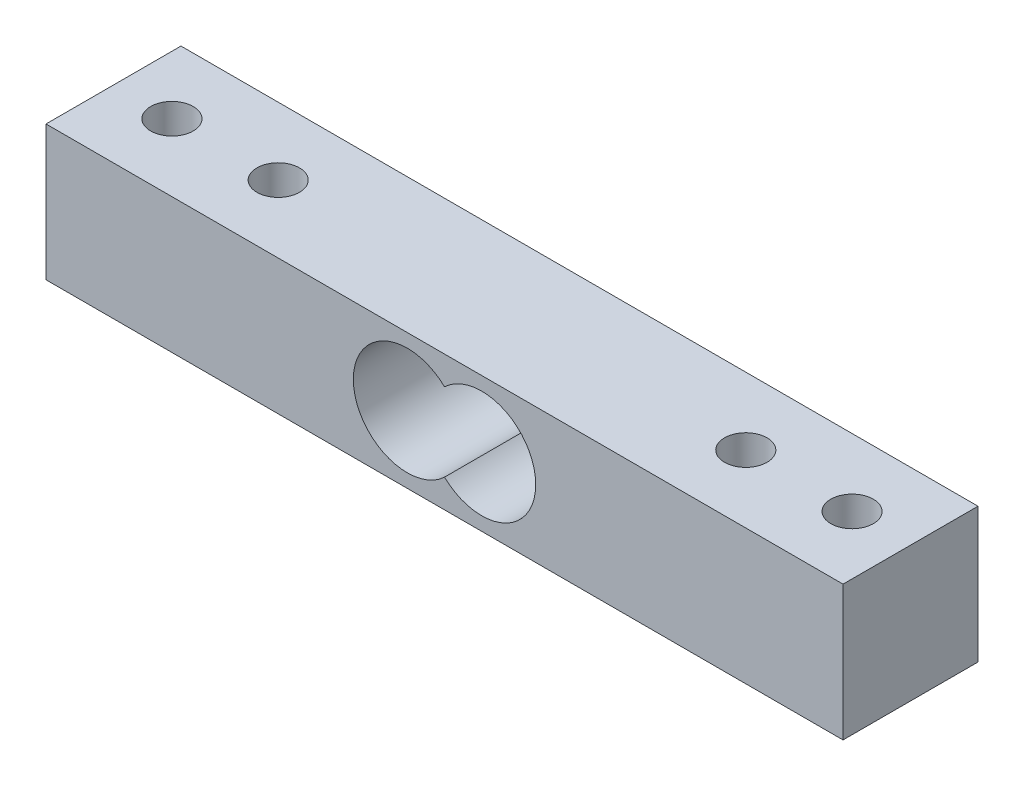
SolidWorks part; units mm, degrees
ref_plane "Front Plane" through (0, 0, 0) normal (0, 0, 1) x (1, 0, 0)
ref_plane "Top Plane" through (0, 0, 0) normal (0, 1, 0) x (1, 0, 0)
ref_plane "Right Plane" through (0, 0, 0) normal (1, 0, 0) x (0, 0, -1)
sketch "Sketch1" plane through (0, 0, 0) normal (0, 0, 1) x (1, 0, 0)
  line L0 (-3.5, 0) -> (3.5, 0) construction
  line L1 (-37.5, 6.35) -> (37.5, 6.35)
  line L2 (-37.5, 6.35) -> (-37.5, -6.35)
  line L3 (-37.5, -6.35) -> (37.5, -6.35)
  line L4 (37.5, 6.35) -> (37.5, -6.35)
  arc A0 (0, 3.6819) -> (0, -3.6819) centre (-3.5, 0) ccw
  arc A1 (0, -3.6819) -> (0, 3.6819) centre (3.5, 0) ccw
  point P4 (0, 6.35)
  point P5 (37.5, 0)
  point P11 (-13.734, 0)
  point P12 (0, 0)
  dimension "D4" = 10.16
  dimension "D1" = 75
  dimension "D2" = 12.7
  dimension "D3" = 7
extrude "LoadCell" add sketch "Sketch1" along normal mid plane 12.7
sketch "Sketch2" plane through (0, 0, 0) normal (0, 1, 0) x (1, 0, 0)
  line L0 (0, 0) -> (0, -5.2506) construction
  circle A2 centre (-32, 0) radius 2
  circle A3 centre (-22, 0) radius 2
  circle A4 centre (32, 0) radius 2
  circle A5 centre (22, 0) radius 2
  point P2 (0, -5.2506)
  dimension "D1" = 4
  dimension "D2" = 4
  dimension "D3" = 10
  dimension "D4" = 22
extrude "Cut-Extrude1" cut sketch "Sketch2" against normal through all both and the other way through all
equation "\"D1@Sketch2\"=\"D2@Sketch2\""
